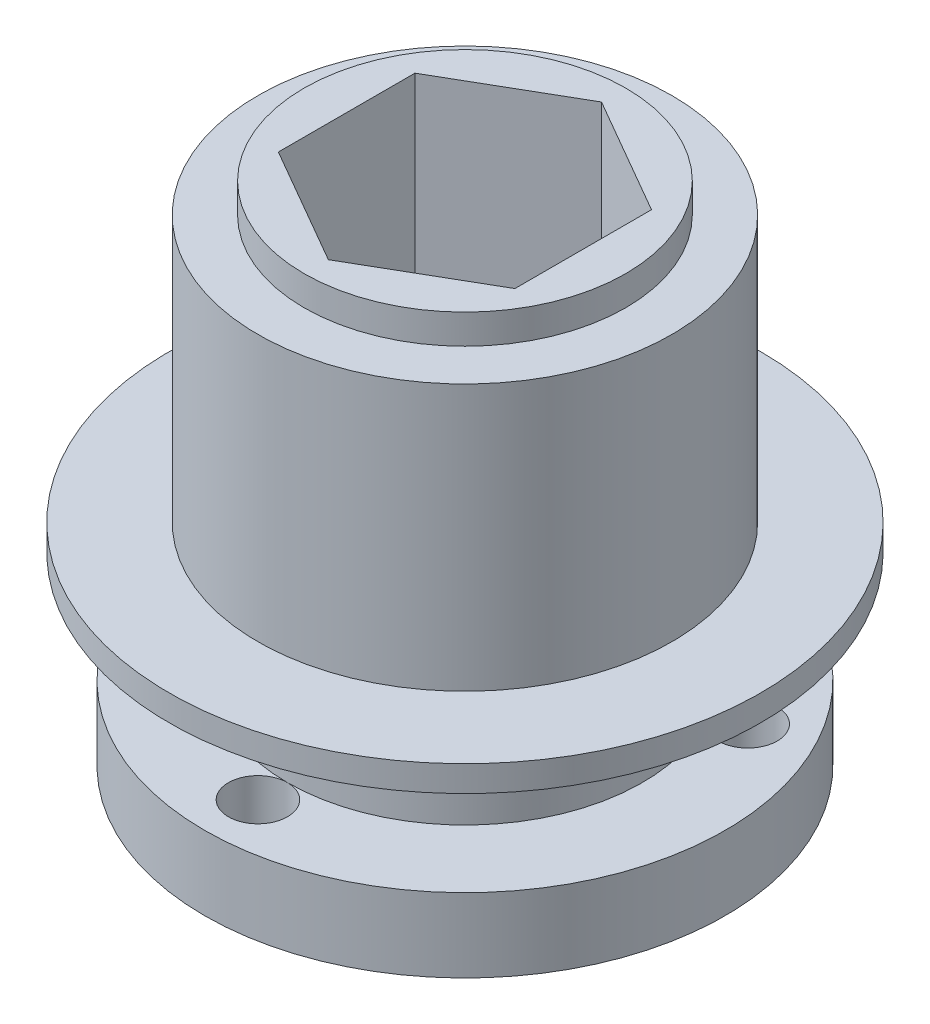
SolidWorks part; units mm, degrees
ref_plane "Front Plane" through (0, 0, 0) normal (0, 0, 1) x (1, 0, 0)
ref_plane "Top Plane" through (0, 0, 0) normal (0, 1, 0) x (1, 0, 0)
ref_plane "Right Plane" through (0, 0, 0) normal (1, 0, 0) x (0, 0, -1)
sketch "Sketch1" plane through (0, 0, 0) normal (0, 0, 1) x (1, 0, 0)
  line L0 (0, -73.2459) -> (0, 114.5694) construction
  line L1 (0, 0) -> (27.94, 0)
  line L2 (27.94, 0) -> (27.94, 7.9375)
  line L3 (27.94, 7.9375) -> (19.05, 7.9375)
  line L4 (19.05, 7.9375) -> (19.05, 19.8438)
  line L5 (19.05, 19.8438) -> (31.75, 19.8438)
  line L6 (31.75, 19.8438) -> (31.75, 22.6219)
  line L7 (31.75, 22.6219) -> (22.225, 22.6219)
  line L8 (22.225, 22.6219) -> (22.225, 51.1969)
  line L9 (22.225, 51.1969) -> (17.2641, 51.1969)
  line L10 (17.2641, 51.1969) -> (17.2641, 54.3719)
  line L11 (17.2641, 54.3719) -> (0, 54.3719)
  line L12 (0, 0) -> (0, 54.3719)
  point P14 (26.9875, 22.6219)
  dimension "D1" = 7.9375
  dimension "D2" = 19.05
  dimension "D3" = 31.75
  dimension "D4" = 22.225
  dimension "D5" = 17.2641
  dimension "D6" = 22.6219
  dimension "D7" = 2.7781
  dimension "D8" = 28.575
  dimension "D9" = 3.175
revolve "Revolve1" add sketch "Sketch1" angle 360 about L12
sketch "Sketch2" plane through (0, 0, 0) normal (0, -1, 0) x (1, 0, 0)
  line L1 (12.7, 7.3323) -> (0, 14.6647)
  line L2 (0, 14.6647) -> (-12.7, 7.3323)
  line L3 (-12.7, 7.3323) -> (-12.7, -7.3323)
  line L4 (-12.7, -7.3323) -> (0, -14.6647)
  line L5 (0, -14.6647) -> (12.7, -7.3323)
  line L6 (12.7, -7.3323) -> (12.7, 7.3323)
  circle A0 centre (0, 0) radius 12.7 construction
  point P1 (0, 14.6647)
  dimension "D1" = 25.4
extrude "Cut-Extrude1" cut sketch "Sketch2" against normal blind 101.6
sketch "Sketch3" plane through (0, 0, 0) normal (0, -1, 0) x (1, 0, 0)
  circle A0 centre (0, 0) radius 22.225 construction
  circle A1 centre (0, 22.225) radius 3.175
  circle A2 centre (19.2474, -11.1125) radius 3.175
  circle A3 centre (-19.2474, -11.1125) radius 3.175
  point P12 (0, 0)
  dimension "D1" = 44.45
  dimension "D2" = 6.35
  dimension "D3" = 3
extrude "Cut-Extrude2" cut sketch "Sketch3" against normal blind 12.7
